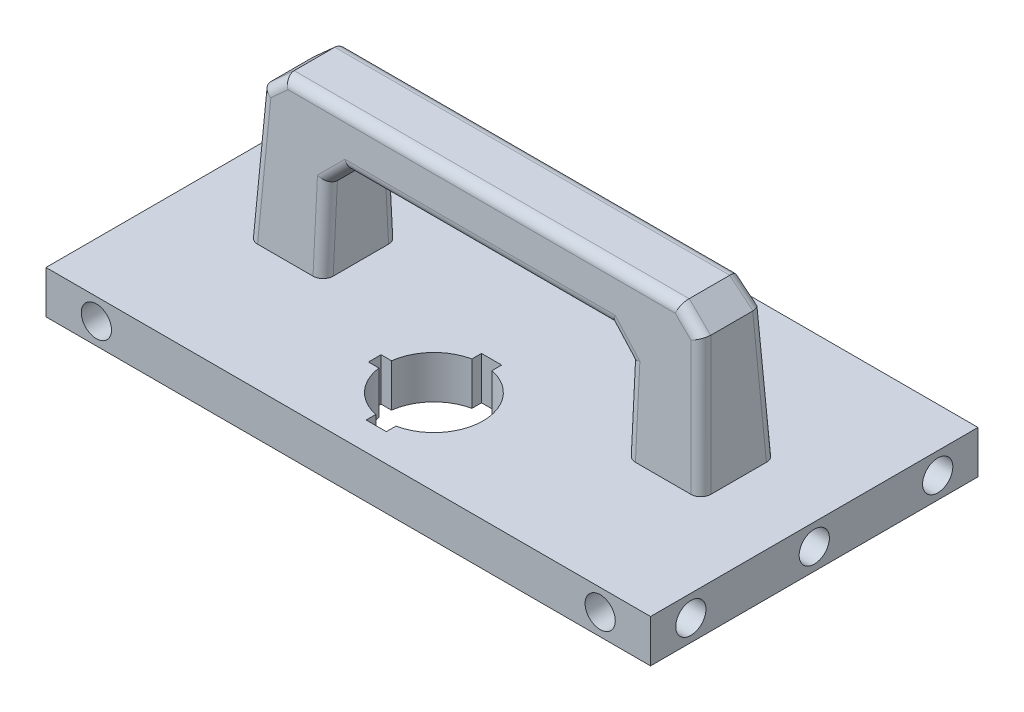
SolidWorks part; units mm, degrees
ref_plane "Front Plane" through (0, 0, 0) normal (0, 0, 1) x (1, 0, 0)
ref_plane "Top Plane" through (0, 0, 0) normal (0, 1, 0) x (1, 0, 0)
ref_plane "Right Plane" through (0, 0, 0) normal (1, 0, 0) x (0, 0, -1)
sketch "Sketch1" plane through (0, 0, 0) normal (1, 0, 0) x (0, 0, -1)
  line L1 (-32.5, -4.25) -> (32.5, -4.25)
  line L2 (-32.5, -4.25) -> (-32.5, 4.25)
  line L3 (-32.5, 4.25) -> (32.5, 4.25)
  line L4 (32.5, -4.25) -> (32.5, 4.25)
  line L5 (-32.5, -4.25) -> (32.5, 4.25) construction
  line L6 (-32.5, 4.25) -> (32.5, -4.25) construction
  point P0 (0, 0)
  dimension "D1" = 8.5
  dimension "D2" = 65
extrude "Boss-Extrude1" add sketch "Sketch1" along normal blind 120
hole_wizard "Ø6.0mm Dowel Hole1" positions "Sketch2" profile "Sketch3" hole size "Ø6.0" standard "ANSI Metric"
sketch "Sketch2" plane through (120, 0, 0) normal (1, 0, 0) x (0, 0, -1)
  line L0 (-32.5, 4.25) -> (-32.5, -4.25) construction
  line L1 (32.5, -4.25) -> (32.5, 4.25) construction
  point P0 (-24.5, 0)
  point P2 (0, 0)
  point P5 (24.5, 0)
  dimension "D1" = 8
  dimension "D2" = 8
sketch "Sketch3" plane through (120, 0, 24.5) normal (0, 1, 0) x (0, 0, -1)
  line L0 (0, 0) -> (0, 11.8026)
  line L1 (0, 11.8026) -> (3, 10)
  line L2 (3, 10) -> (3, 0)
  line L5 (3, 0) -> (0, 0)
  line L10 (0, 11.8026) -> (-3, 10) construction
  line L11 (0, -6.35) -> (0, 107.95) construction
  dimension "Hole Dia." = 6
  dimension "Hole Depth" = 10
  dimension "Drill Angle" = 118
ref_plane "Plane1" through (60, 0, 0) normal (1, 0, 0) x (0, 0, -1)
mirror "Mirror1" about plane through (60, 0, 0) normal (1, 0, 0) of "Ø6.0mm Dowel Hole1"
sketch "Sketch4" plane through (0, 4.25, 0) normal (0, 1, 0) x (1, 0, 0)
  line L0 (120, -32.5) -> (0, -32.5) construction
  line L1 (105, 7.5) -> (15, 7.5)
  line L2 (105, 7.5) -> (105, -7.5)
  line L3 (105, -7.5) -> (15, -7.5)
  line L4 (15, 7.5) -> (15, -7.5)
  line L5 (105, 7.5) -> (15, -7.5) construction
  line L6 (105, -7.5) -> (15, 7.5) construction
  line L7 (120, 32.5) -> (120, -32.5) construction
  point P0 (60, 0)
  point P8 (60, -32.5)
  point P11 (120, 0)
  dimension "D1" = 15
  dimension "D2" = 90
extrude "Boss-Extrude2" add sketch "Sketch4" along normal blind 30 draft 3
sketch "Sketch5" plane through (0, 0, 0) normal (0, 0, 1) x (1, 0, 0)
  line L1 (90, 4.25) -> (30, 4.25)
  line L2 (90, 4.25) -> (90, 24.25)
  line L3 (90, 24.25) -> (30, 24.25)
  line L4 (15, 4.25) -> (105, 4.25)
  line L5 (16.5722, 34.25) -> (15, 4.25)
  line L6 (103.4278, 34.25) -> (16.5722, 34.25)
  line L7 (105, 4.25) -> (103.4278, 34.25)
  line L8 (15, 4.25) -> (105, 4.25)
  line L9 (16.5722, 34.25) -> (15, 4.25)
  line L10 (103.4278, 34.25) -> (16.5722, 34.25)
  line L11 (105, 4.25) -> (103.4278, 34.25)
  line L12 (30, 4.25) -> (30, 24.25)
  dimension "D2" = 15
  dimension "D3" = 15
  dimension "D4" = 20
  dimension "D1" = 0
extrude "Cut-Extrude1" cut sketch "Sketch5" against normal through all both and the other way through all contours L12 L1 L2 L3
chamfer "Chamfer1" distance 4 angle 45 4 edges at (30, 24.25, 0) (90, 24.25, 0) (103.4278, 34.25, 0) (16.5722, 34.25, 0)
fillet "Fillet1" radius 2 20 edges at (88, 22.25, 6.5567) (60, 24.25, 6.4518) (90, 12.25, 7.0807) (30, 12.25, 7.0807) (32, 22.25, 6.5567) (88, 22.25, -6.5567) (90, 12.25, -7.0807) (60, 24.25, -6.4518) (32, 22.25, -6.5567) (30, 12.25, -7.0807) (18.5811, 32.2527, 6.0324) (15.6814, 17.2527, 6.8186) (15.6814, 17.2527, -6.8186) (18.5811, 32.2527, -6.0324) (101.4189, 32.2527, 6.0324) (101.4189, 32.2527, -6.0324) (104.3186, 17.2527, 6.8186) (104.3186, 17.2527, -6.8186) (60, 34.25, 5.9278) (60, 34.25, -5.9278)
hole_wizard "Ø6.0mm Dowel Hole2" positions "Sketch6" profile "Sketch7" hole size "Ø6.0" standard "ANSI Metric"
sketch "Sketch6" plane through (0, 0, -32.5) normal (0, 0, -1) x (-1, 0, 0)
  line L0 (-120, -4.25) -> (-120, 4.25) construction
  line L1 (0, -4.25) -> (0, 4.25) construction
  line L2 (-120, 0) -> (0, 0) construction
  point P0 (-110, 0)
  point P2 (-10, 0)
  dimension "D1" = 10
  dimension "D2" = 10
sketch "Sketch7" plane through (110, 0, -32.5) normal (1, 0, 0) x (0, 1, 0)
  line L0 (0, 0) -> (0, 9.8026)
  line L1 (0, 9.8026) -> (3, 8)
  line L2 (3, 8) -> (3, 0)
  line L5 (3, 0) -> (0, 0)
  line L10 (0, 9.8026) -> (-3, 8) construction
  line L11 (0, -6.35) -> (0, 107.95) construction
  dimension "Hole Dia." = 6
  dimension "Hole Depth" = 8
  dimension "Drill Angle" = 118
mirror "Mirror2" about plane through (0, 0, 0) normal (0, 0, 1) of "Ø6.0mm Dowel Hole2"
ref_plane "Plane3" through (0, 4.25, 0) normal (0, 1, 0) x (1, 0, 0)
split "Split1" trim tools "Plane3" bodies to split 108 resulting bodies 112 113
hole_wizard "CSK for M4 Flat Head Machine Screw1" positions "Sketch8" profile "Sketch9" countersink size "M4" standard "ANSI Metric"
sketch "Sketch8" plane through (0, -4.25, 0) normal (0, -1, 0) x (-1, 0, 0)
  line L0 (-92, -7.5) -> (-103.0027, -7.5) construction
  line L1 (-90, 5.4973) -> (-90, -5.4973) construction
  line L2 (-103.0027, 7.5) -> (-92, 7.5) construction
  line L3 (-105, -5.5027) -> (-105, 5.5027) construction
  line L4 (-15, 5.5027) -> (-15, -5.5027) construction
  line L5 (-16.9973, -7.5) -> (-28, -7.5) construction
  line L6 (-30, 5.4973) -> (-30, -5.4973) construction
  line L7 (-28, 7.5) -> (-16.9973, 7.5) construction
  line L8 (-92, -7.5) -> (-103.0027, -7.5)
  line L9 (-90, 5.4973) -> (-90, -5.4973)
  line L10 (-103.0027, 7.5) -> (-92, 7.5)
  line L11 (-105, -5.5027) -> (-105, 5.5027)
  line L12 (-15, 5.5027) -> (-15, -5.5027)
  line L13 (-16.9973, -7.5) -> (-28, -7.5)
  line L14 (-30, 5.4973) -> (-30, -5.4973)
  line L15 (-28, 7.5) -> (-16.9973, 7.5)
  point P0 (-97.5014, 0)
  point P2 (-22.4986, 0)
  point P22 (-97.5014, -7.5)
  point P24 (-22.4986, -7.5)
  point P26 (-30, 0)
  point P28 (-105, 0)
sketch "Sketch9" plane through (97.5014, -4.25, 0) normal (1, 0, 0) x (0, 0, -1)
  line L0 (0, 0) -> (0, 21.4421)
  line L1 (0, 21.4421) -> (2.4, 20)
  line L2 (2.4, 20) -> (2.4, 2.3)
  line L3 (2.4, 2.3) -> (4.7, 0)
  line L5 (4.7, 0) -> (0, 0)
  line L6 (-2.4, 2.3) -> (-4.7, 0) construction
  line L10 (0, 21.4421) -> (-2.4, 20) construction
  line L11 (0, -6.35) -> (0, 107.95) construction
  dimension "Hole Dia." = 4.8
  dimension "Hole Depth" = 20
  dimension "Near C'Sink Dia." = 9.4
  dimension "Near C'Sink Angle" = 90
  dimension "Drill Angle" = 118
sketch "Sketch10" plane through (0, 4.25, 0) normal (0, 1, 0) x (1, 0, 0)
  line L0 (120, -32.5) -> (0, -32.5) construction
  line L1 (48.25, -16.75) -> (52.25, -16.75)
  line L2 (48.25, -16.75) -> (48.25, -14.25)
  line L3 (48.25, -14.25) -> (52.25, -14.25)
  line L4 (52.25, -16.75) -> (52.25, -14.25)
  line L5 (48.25, -16.75) -> (52.25, -14.25) construction
  line L6 (48.25, -14.25) -> (52.25, -16.75) construction
  line L7 (62, -26.95) -> (58, -26.95)
  line L8 (62, -26.95) -> (62, -23.55)
  line L9 (62, -23.55) -> (58, -23.55)
  line L10 (58, -26.95) -> (58, -23.55)
  line L11 (62, -26.95) -> (58, -23.55) construction
  line L12 (62, -23.55) -> (58, -26.95) construction
  line L13 (62, -4.05) -> (58, -4.05)
  line L14 (62, -4.05) -> (62, -7.45)
  line L15 (62, -7.45) -> (58, -7.45)
  line L16 (58, -4.05) -> (58, -7.45)
  line L17 (62, -4.05) -> (58, -7.45) construction
  line L18 (62, -7.45) -> (58, -4.05) construction
  circle A0 centre (60, -15.5) radius 9.75
  point P2 (50.25, -15.5)
  point P7 (60, -25.25)
  point P12 (60, -5.75)
  point P21 (60, -32.5)
  dimension "D1" = 19.5
  dimension "D2" = 2.5
  dimension "D3" = 2
  dimension "D4" = 4
  dimension "D5" = 4
  dimension "D6" = 1.7
  dimension "D7" = 1.7
  dimension "D8" = 17
extrude "Cut-Extrude2" cut sketch "Sketch10" against normal through all contours A0 L3 L2 L1 | L8 A0 L14 L15 L16 L3 L4 L1 L10 L9 | L10 A0 L8 L9 | A0 L10 L7 L8 | L3 A0 L1 L4 | A0 L14 L13 L16 | L14 A0 L16 L15
